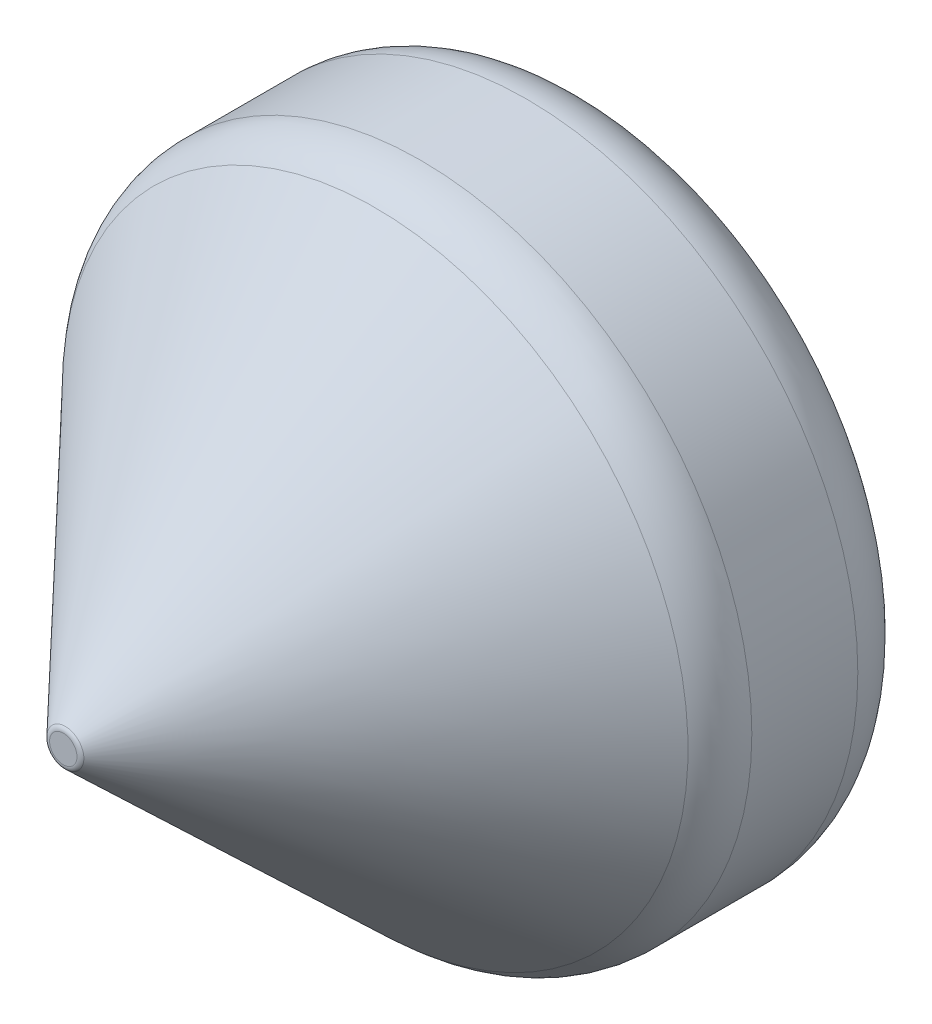
SolidWorks part; units mm, degrees
ref_plane "Front Plane" through (0, 0, 0) normal (0, 0, 1) x (1, 0, 0)
ref_plane "Top Plane" through (0, 0, 0) normal (0, 1, 0) x (1, 0, 0)
ref_plane "Right Plane" through (0, 0, 0) normal (1, 0, 0) x (0, 0, -1)
sketch "Sketch2" plane through (0, 0, 0) normal (0, 0, 1) x (1, 0, 0)
  circle A0 centre (0, 0) radius 50
extrude "Boss-Extrude1" add sketch "Sketch2" along normal blind 30
ref_plane "Plane1" through (0, 0, 80) normal (0, 0, 1) x (1, 0, 0)
sketch "Sketch4" plane through (0, 0, 80) normal (0, 0, 1) x (1, 0, 0)
  circle A0 centre (0, 0) radius 2.5
loft "Loft2" add profiles "Sketch4" section edge at (50, 0, 30) section "Sketch4"
fillet "Fillet1" radius 10 1 edges at (50, 0, 30)
fillet "Fillet3" radius 1 1 edges at (2.5, 0, 80)
sketch "Sketch6" plane through (0, 0, 0) normal (0, 0, -1) x (-1, 0, 0)
  circle A0 centre (0, 0) radius 13
extrude "Boss-Extrude2" add sketch "Sketch6" along normal blind 12
sketch "Sketch7" plane through (0, 0, -12) normal (0, 0, -1) x (-1, 0, 0)
  circle A0 centre (0, 0) radius 12
extrude "Cut-Extrude1" cut sketch "Sketch7" against normal blind 12
sketch "Sketch8" plane through (0, 0, 0) normal (1, 0, 0) x (0, 0, -1)
  circle A0 centre (7.94, 0) radius 2
extrude "Cut-Extrude2" cut sketch "Sketch8" against normal blind 19 and the other way blind 20
sketch "Sketch9" plane through (0, 0, 0) normal (1, 0, 0) x (0, 0, -1)
  line L1 (12, -13) -> (12, 13) construction
  line L2 (0, 0) -> (0, 3) construction
  line L3 (0, 3) -> (12, 3)
  line L4 (12, 3) -> (12, 13)
  line L5 (12, 13) -> (0, 13)
  line L6 (0, 13) -> (0, 3)
  line L7 (12, -13) -> (0, -13)
  line L8 (12, -3) -> (12, -13)
  line L9 (0, -3) -> (12, -3)
  line L10 (0, -13) -> (0, -3)
extrude "Cut-Extrude3" cut sketch "Sketch9" against normal blind 23 and the other way blind 17
fillet "Fillet4" radius 10 1 edges at (50, 0, 0)
